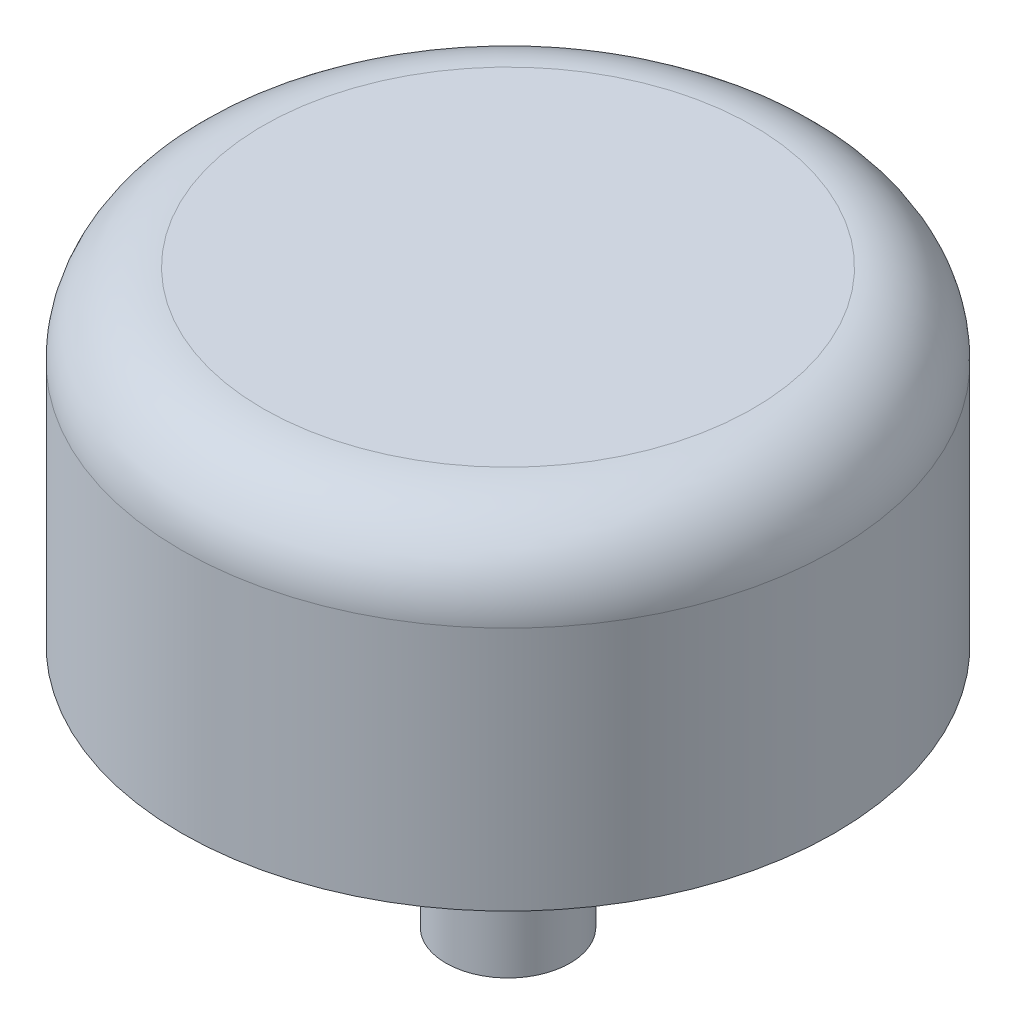
SolidWorks part; units mm, degrees
material "Rubber"
ref_plane "Front-Back Midplane" through (0, 0, 0) normal (0, 0, 1) x (1, 0, 0)
ref_plane "Horizontal Midplane" through (0, 0, 0) normal (0, 1, 0) x (1, 0, 0)
ref_plane "Left-Right Midplane" through (0, 0, 0) normal (1, 0, 0) x (0, 0, -1)
ref_axis "Axis1" through (0, 52.5, 0) along (0, -1, 0)
sketch "Sketch1" plane through (0, 0, 0) normal (0, 0, 1) x (1, 0, 0)
  line L0 (0, -9.525) -> (-2.413, -9.525)
  line L1 (-2.413, -9.525) -> (-2.413, 0)
  line L2 (-2.413, 0) -> (-12.7, 0)
  line L3 (-12.7, 0) -> (-12.7, 9.525)
  line L4 (-9.525, 12.7) -> (0, 12.7)
  line L5 (0, 12.7) -> (0, -9.525)
  arc A0 (-12.7, 9.525) -> (-9.525, 12.7) centre (-9.525, 9.525) cw
  point P9 (-12.7, 12.7)
  dimension "D5" = 3.175
  dimension "D1" = 12.7
  dimension "D2" = 12.7
  dimension "D3" = 9.525
  dimension "D4" = 2.413
revolve "Revolve1" add sketch "Sketch1" angle 360 about axis through (0, 52.5, 0) along (0, -1, 0)
